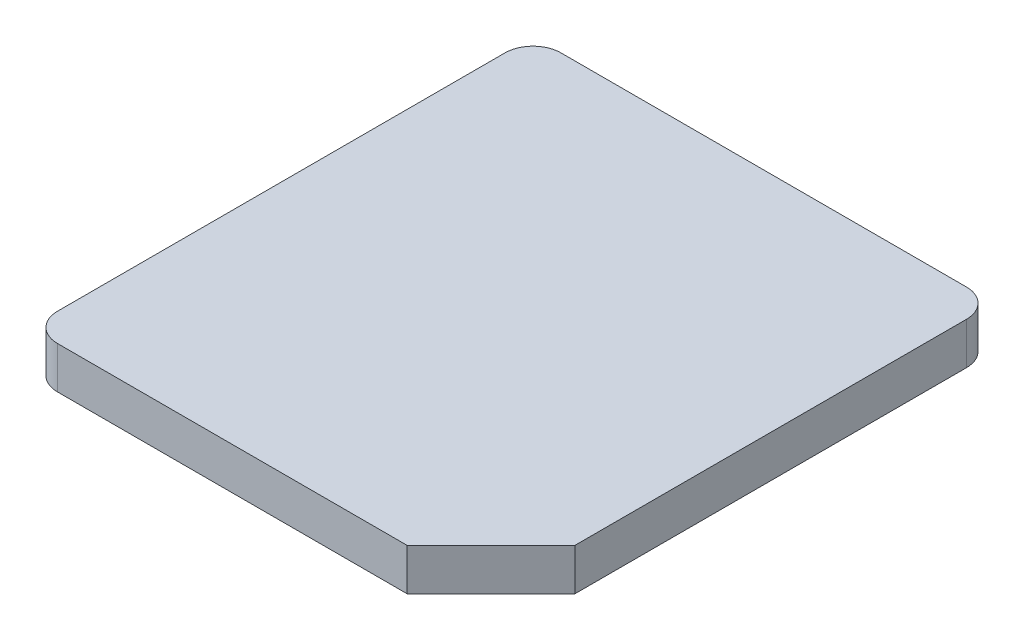
SolidWorks part; units mm, degrees
ref_plane "Front Plane" through (0, 0, 0) normal (0, 0, 1) x (1, 0, 0)
ref_plane "Top Plane" through (0, 0, 0) normal (0, 1, 0) x (1, 0, 0)
ref_plane "Right Plane" through (0, 0, 0) normal (1, 0, 0) x (0, 0, -1)
sketch "Sketch1" plane through (0, 0, 0) normal (0, 1, 0) x (1, 0, 0)
  line L1 (-0.825, 0.9) -> (0.825, 0.9)
  line L2 (-0.825, 0.9) -> (-0.825, -0.9)
  line L3 (-0.825, -0.9) -> (0.825, -0.9)
  line L4 (0.825, 0.9) -> (0.825, -0.9)
  line L5 (-0.825, 0.9) -> (0.825, -0.9) construction
  line L6 (-0.825, -0.9) -> (0.825, 0.9) construction
  point P0 (0, 0)
  dimension "D1" = 1.65
  dimension "D2" = 1.8
extrude "Boss-Extrude1" add sketch "Sketch1" along normal blind 0.15
sketch "Sketch2" plane through (0, 0.15, 0) normal (0, 1, 0) x (1, 0, 0)
  line L0 (0.525, -0.9) -> (0.825, -0.6)
  line L1 (-0.825, -0.9) -> (0.825, -0.9) construction
  line L2 (0.825, -0.9) -> (0.825, 0.9) construction
  line L3 (0.825, -0.6) -> (0.825, -0.9)
  line L4 (0.825, -0.9) -> (0.525, -0.9)
  dimension "D1" = 0.3
extrude "Cut-Extrude1" cut sketch "Sketch2" against normal through all
fillet "Fillet1" radius 0.1 3 edges at (0.825, 0.075, -0.9) (-0.825, 0.075, -0.9) (-0.825, 0.075, 0.9)
